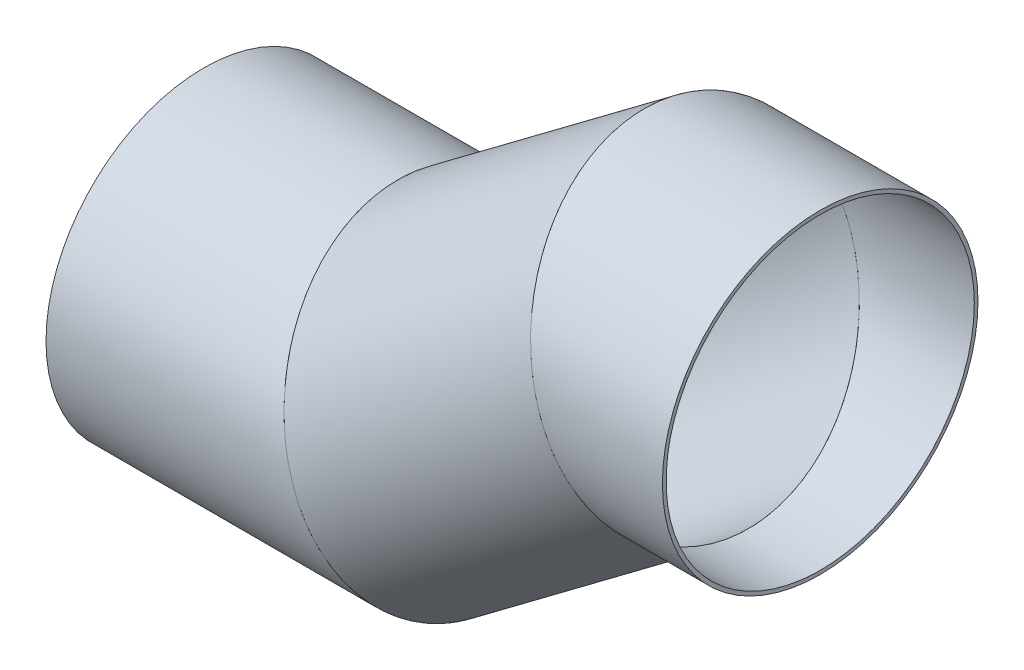
SolidWorks part; units mm, degrees
material "1.0038 (S235JRG2)"
ref_plane "Vorne" through (0, 0, 0) normal (0, 0, 1) x (1, 0, 0)
ref_plane "Oben" through (0, 0, 0) normal (0, 1, 0) x (1, 0, 0)
ref_plane "Rechts" through (0, 0, 0) normal (1, 0, 0) x (0, 0, -1)
sketch "Skizze1" plane through (0, 0, 0) normal (0, 0, 1) x (1, 0, 0)
  line L0 (0, 0) -> (200, 0)
  line L1 (200, 0) -> (400, 150)
  line L2 (400, 150) -> (500, 150)
  dimension "D1" = 200
  dimension "D2" = 150
  dimension "D3" = 100
  dimension "D4" = 500
other "Strukturbauteil1"
ref_plane "Ebene1" through (0, 0, 0) normal (1, 0, 0) x (0, 1, 0)
sketch "Sketch1" plane through (0, 0, 0) normal (1, 0, 0) x (0, 1, 0)
  circle A0 centre (0, 0) radius 125
  circle A1 centre (0, 0) radius 128
  point P3 (0, 0)
  dimension "In_dia" = 250
  dimension "Out_dia" = 256
